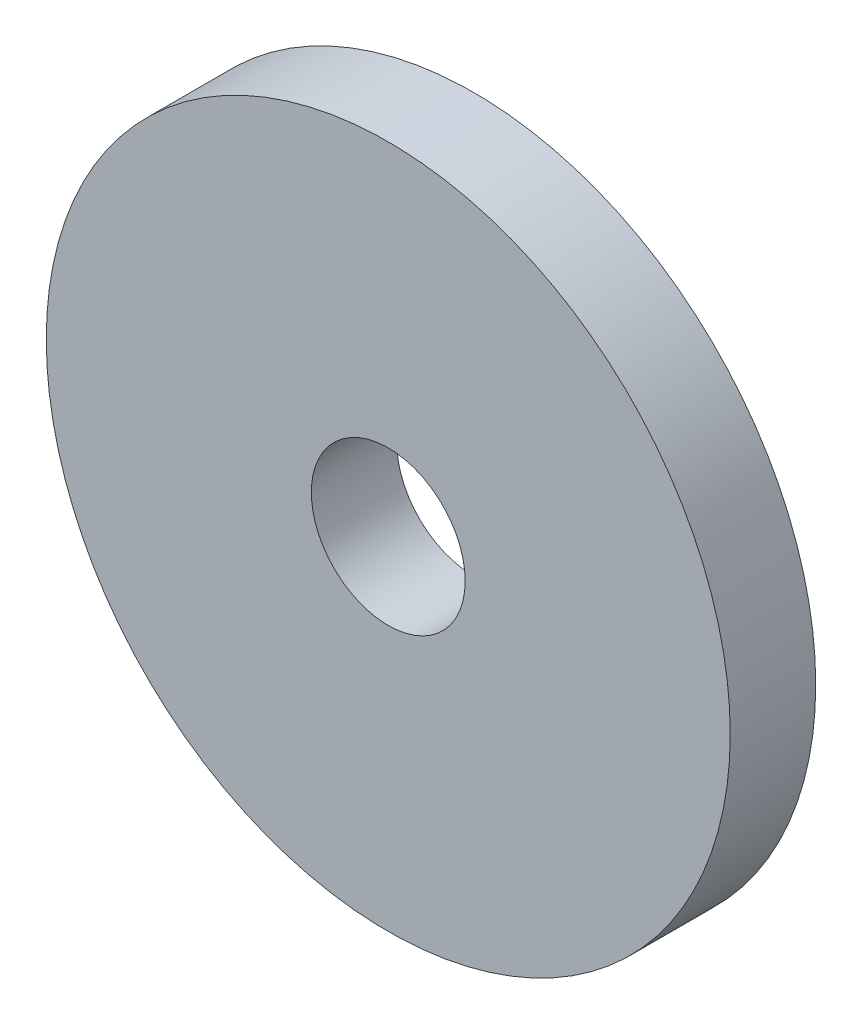
SolidWorks part; units mm, degrees
ref_plane "Front Plane" through (0, 0, 0) normal (0, 0, 1) x (1, 0, 0)
ref_plane "Top Plane" through (0, 0, 0) normal (0, 1, 0) x (1, 0, 0)
ref_plane "Right Plane" through (0, 0, 0) normal (1, 0, 0) x (0, 0, -1)
sketch "Sketch1" plane through (0, 0, 0) normal (0, 0, 1) x (1, 0, 0)
  circle A0 centre (0, 0) radius 20
  dimension "D1" = 40
extrude "Boss-Extrude1" add sketch "Sketch1" along normal blind 5
sketch "Sketch2" plane through (0, 0, 5) normal (0, 0, 1) x (1, 0, 0)
  circle A0 centre (0, 0) radius 4.5
  dimension "D1" = 9
extrude "Cut-Extrude1" cut sketch "Sketch2" against normal blind 5
